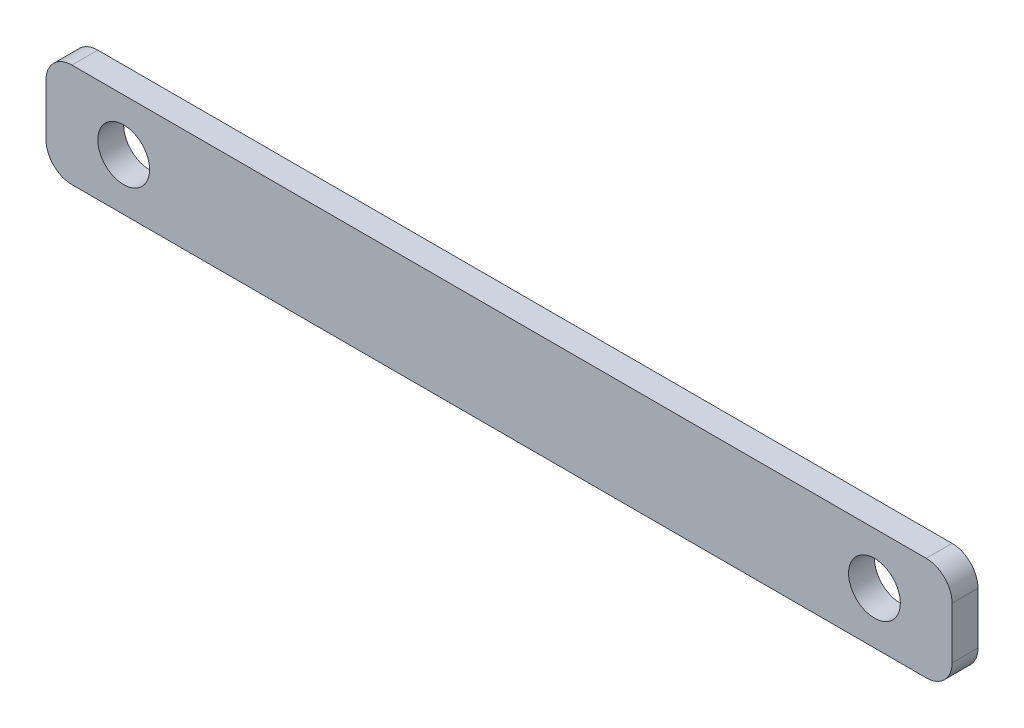
SolidWorks part; units mm, degrees
ref_plane "Front Plane" through (0, 0, 0) normal (0, 0, 1) x (1, 0, 0)
ref_plane "Top Plane" through (0, 0, 0) normal (0, 1, 0) x (1, 0, 0)
ref_plane "Right Plane" through (0, 0, 0) normal (1, 0, 0) x (0, 0, -1)
sketch "Sketch1" plane through (0, 0, 0) normal (0, 0, 1) x (1, 0, 0)
  line L0 (-200, 151.9947) -> (-170, 151.9947) construction
  line L2 (-190, 151.9947) -> (140, 151.9947)
  line L3 (-200, 141.9947) -> (-200, 121.9947)
  line L4 (-190, 111.9947) -> (140, 111.9947)
  line L5 (150, 141.9947) -> (150, 121.9947)
  line L6 (-200, 151.9947) -> (150, 111.9947) construction
  line L7 (-200, 111.9947) -> (150, 151.9947) construction
  line L8 (150, 151.9947) -> (120, 151.9947) construction
  line L9 (-170, 151.9947) -> (-170, 111.9947) construction
  line L10 (120, 151.9947) -> (120, 111.9947) construction
  arc A0 (140, 111.9947) -> (150, 121.9947) centre (140, 121.9947) ccw
  arc A1 (140, 151.9947) -> (150, 141.9947) centre (140, 141.9947) cw
  arc A2 (-200, 121.9947) -> (-190, 111.9947) centre (-190, 121.9947) ccw
  arc A3 (-190, 151.9947) -> (-200, 141.9947) centre (-190, 141.9947) ccw
  circle A4 centre (-170, 131.9947) radius 10
  circle A5 centre (120, 131.9947) radius 10
  point P0 (-25, 131.9947)
  dimension "D3" = 10
  dimension "D1" = 350
  dimension "D2" = 40
extrude "Boss-Extrude1" add sketch "Sketch1" along normal mid plane 10
